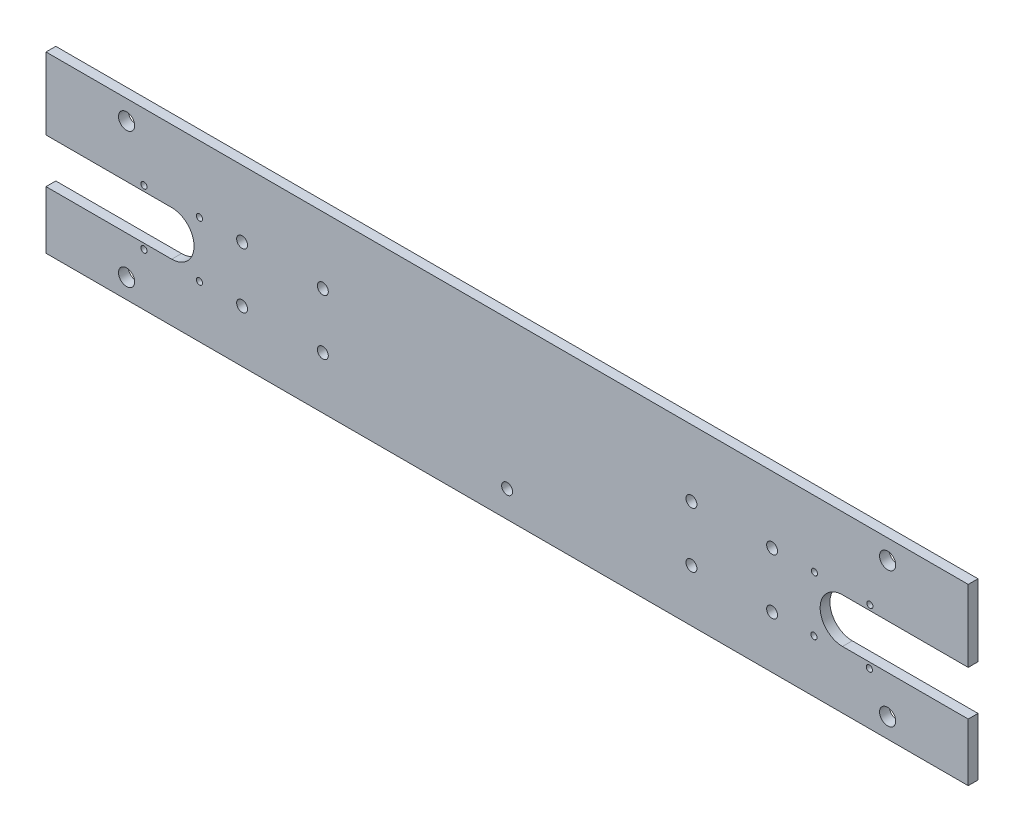
SolidWorks part; units mm, degrees
material "ABS"
ref_plane "X-Y Datum" through (0, 0, 0) normal (0, 0, 1) x (1, 0, 0)
ref_plane "X-Z Datum" through (0, 0, 0) normal (0, 1, 0) x (1, 0, 0)
ref_plane "Y-Z Datum" through (0, 0, 0) normal (1, 0, 0) x (0, 0, -1)
sketch "Sketch1" plane through (0, 0, 0) normal (0, 0, 1) x (1, 0, 0)
  line L1 (13.0279, 139.5112) -> (312.4261, 139.5112)
  line L2 (13.0279, 139.5112) -> (13.0279, 82.9123)
  line L3 (13.0279, 82.9123) -> (312.4261, 82.9123)
  line L4 (312.4261, 139.5112) -> (312.4261, 82.9123)
  circle A0 centre (286.2666, 133.1612) radius 2.625
  circle A1 centre (286.2666, 89.2623) radius 2.625
  circle A2 centre (39.1874, 133.1612) radius 2.625
  circle A3 centre (39.1874, 89.2623) radius 2.625
extrude "Boss-Extrude1" add sketch "Sketch1" along normal blind 3.175
sketch "Sketch2" plane through (0, 0, 3.175) normal (0, 0, 1) x (1, 0, 0)
  line L4 (53.8457, 117.909) -> (53.8457, 99.909) construction
  line L5 (13.0279, 139.5112) -> (13.0279, 82.9123) construction
  line L6 (13.0279, 139.5112) -> (312.4261, 139.5112) construction
  line L7 (312.4261, 139.5112) -> (312.4261, 82.9123) construction
  line L8 (13.0279, 82.9123) -> (312.4261, 82.9123) construction
  line L9 (44.8457, 99.909) -> (62.8457, 99.909) construction
  line L10 (44.8457, 99.909) -> (44.8457, 117.909) construction
  line L11 (44.8457, 117.909) -> (62.8457, 117.909) construction
  line L12 (62.8457, 99.909) -> (62.8457, 117.909) construction
  circle A16 centre (280.5042, 117.8243) radius 1
  circle A17 centre (280.3353, 99.8251) radius 1
  circle A18 centre (262.5049, 117.9932) radius 1
  circle A19 centre (262.3361, 99.994) radius 1
  circle A20 centre (62.8457, 117.909) radius 1
  circle A21 centre (62.8457, 99.909) radius 1
  circle A22 centre (44.8457, 117.909) radius 1
  circle A23 centre (44.8457, 99.909) radius 1
  point P20 (13.0279, 139.5112)
extrude "Cut-Extrude1" cut sketch "Sketch2" against normal through all
sketch "Sketch3" plane through (0, 0, 3.175) normal (0, 0, 1) x (1, 0, 0)
  line L0 (116.245, 82.9123) -> (116.245, 122.2084) construction
  line L1 (116.245, 82.9123) -> (209.209, 82.9123) construction
  line L2 (209.209, 82.9123) -> (209.209, 122.2084) construction
  line L3 (116.245, 122.2084) -> (209.209, 122.2084) construction
  line L4 (13.0279, 82.9123) -> (312.4261, 82.9123) construction
  line L5 (62.8457, 122.2084) -> (116.245, 122.2084) construction
  line L6 (63.8457, 117.909) -> (89.5454, 117.909) construction
  line L7 (89.5454, 117.909) -> (116.245, 117.909) construction
  line L8 (63.8457, 99.909) -> (89.5454, 99.909) construction
  line L9 (89.5454, 99.909) -> (116.245, 99.909) construction
  line L10 (162.727, 139.5112) -> (162.727, 122.2084) construction
  line L12 (312.4261, 139.5112) -> (13.0279, 139.5112) construction
  line L13 (13.0279, 111.2118) -> (23.6763, 111.2118) construction
  line L14 (13.0279, 139.5112) -> (13.0279, 82.9123) construction
  circle A0 centre (62.8457, 117.909) radius 1 construction
  circle A1 centre (62.8457, 99.909) radius 1 construction
  circle A2 centre (76.6956, 117.909) radius 1.778
  circle A3 centre (76.6956, 99.909) radius 1.778
  circle A4 centre (102.8952, 117.909) radius 1.778
  circle A5 centre (102.8952, 99.909) radius 1.778
  circle A6 centre (248.7585, 99.909) radius 1.778
  circle A7 centre (222.5588, 99.909) radius 1.778
  circle A8 centre (222.5588, 117.909) radius 1.778
  circle A9 centre (248.7585, 117.909) radius 1.778
  circle A11 centre (162.727, 91.5638) radius 1.778
  point P4 (162.727, 82.9123)
extrude "Cut-Extrude2" cut sketch "Sketch3" against normal through all
sketch "Sketch4" plane through (0, 0, 3.175) normal (0, 0, 1) x (1, 0, 0)
  line L0 (42.3057, 121.449) -> (42.3057, 96.369)
  line L1 (13.0279, 139.5112) -> (312.4261, 139.5112)
  line L2 (13.0279, 139.5112) -> (13.0279, 82.9123)
  line L3 (13.0279, 82.9123) -> (312.4261, 82.9123)
  line L4 (312.4261, 139.5112) -> (312.4261, 82.9123)
  line L5 (44.8457, 118.909) -> (62.8457, 118.909) construction
  line L6 (44.8457, 118.909) -> (44.8457, 98.909) construction
  line L7 (44.8457, 98.909) -> (62.8457, 98.909) construction
  line L8 (62.8457, 118.909) -> (62.8457, 98.909) construction
  line L9 (42.3057, 96.369) -> (65.3857, 96.369)
  line L10 (65.3857, 121.449) -> (65.3857, 96.369)
  line L11 (42.3057, 121.449) -> (65.3857, 121.449)
  line L12 (162.727, 139.5112) -> (162.727, 151.1808) construction
  line L13 (283.1483, 121.449) -> (260.0683, 121.449)
  line L14 (260.0683, 121.449) -> (260.0683, 96.369)
  line L15 (283.1483, 96.369) -> (260.0683, 96.369)
  line L16 (283.1483, 121.449) -> (283.1483, 96.369)
  circle A0 centre (76.6956, 117.909) radius 2.54
  circle A1 centre (102.8952, 117.909) radius 2.54
  circle A2 centre (76.6956, 99.909) radius 2.54
  circle A3 centre (102.8952, 99.909) radius 2.54
  circle A4 centre (162.727, 91.5638) radius 2.54
  circle A5 centre (222.5588, 117.909) radius 2.54
  circle A6 centre (222.5588, 99.909) radius 2.54
  circle A7 centre (248.7585, 117.909) radius 2.54
  circle A8 centre (248.7585, 99.909) radius 2.54
  circle A9 centre (44.8457, 117.909) radius 1 construction
  circle A10 centre (62.8457, 99.909) radius 1 construction
  dimension "D1" = 2.54
sketch "Sketch5" plane through (0, 0, 3.175) normal (0, 0, 1) x (1, 0, 0)
  line L0 (53.8457, 117.909) -> (53.8457, 99.909) construction
  line L1 (44.8457, 99.909) -> (62.8457, 99.909) construction
  line L2 (44.8457, 99.909) -> (44.8457, 117.909) construction
  line L3 (44.8457, 117.909) -> (62.8457, 117.909) construction
  line L4 (62.8457, 99.909) -> (62.8457, 117.909) construction
  line L5 (53.8457, 116.1633) -> (13.0279, 116.1633)
  line L6 (13.0279, 139.5112) -> (13.0279, 82.9123) construction
  line L7 (53.8457, 101.6548) -> (13.0279, 101.6548)
  line L8 (13.0279, 101.6548) -> (13.0279, 116.1633)
  line L9 (162.727, 139.5112) -> (162.727, 82.9123) construction
  line L10 (312.4261, 139.5112) -> (13.0279, 139.5112) construction
  line L11 (13.0279, 82.9123) -> (312.4261, 82.9123) construction
  line L12 (271.6083, 101.6548) -> (312.4261, 101.6548)
  line L13 (312.4261, 101.6548) -> (312.4261, 116.1633)
  line L14 (271.6083, 116.1633) -> (312.4261, 116.1633)
  arc A0 (53.8457, 101.6548) -> (53.8457, 116.1633) centre (53.8457, 108.909) ccw
  arc A1 (271.6083, 101.6548) -> (271.6083, 116.1633) centre (271.6083, 108.909) cw
extrude "Cut-Extrude3" cut sketch "Sketch5" against normal through all
